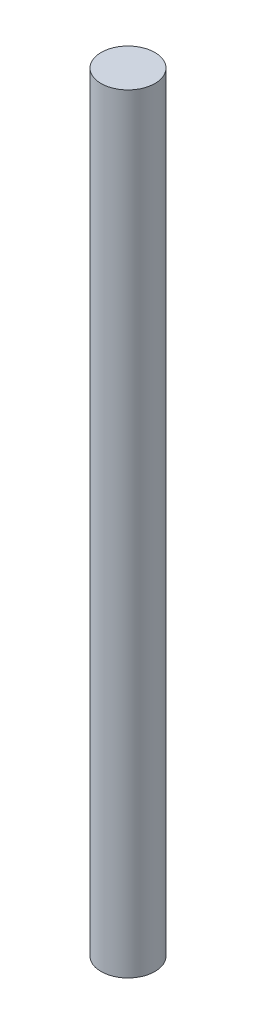
SolidWorks part; units mm, degrees
material "6061-T6 (SS)"
ref_plane "Front Plane" through (0, 0, 0) normal (0, 0, 1) x (1, 0, 0)
ref_plane "Top Plane" through (0, 0, 0) normal (0, 1, 0) x (1, 0, 0)
ref_plane "Right Plane" through (0, 0, 0) normal (1, 0, 0) x (0, 0, -1)
sketch "Sketch1" plane through (0, 0, 0) normal (0, 1, 0) x (1, 0, 0)
  circle A0 centre (0, 0) radius 8
  dimension "D1" = 16
extrude "Boss-Extrude1" add sketch "Sketch1" along normal blind 228.6
